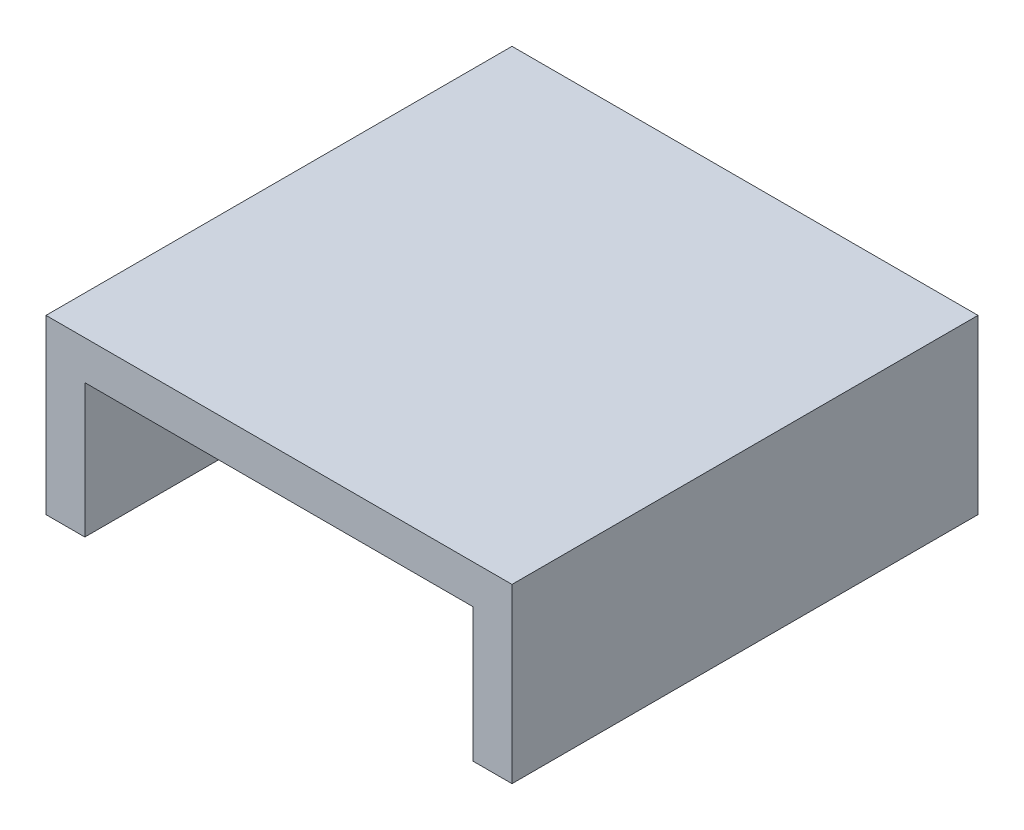
SolidWorks part; units mm, degrees
ref_plane "Front Plane" through (0, 0, 0) normal (0, 0, 1) x (1, 0, 0)
ref_plane "Top Plane" through (0, 0, 0) normal (0, 1, 0) x (1, 0, 0)
ref_plane "Right Plane" through (0, 0, 0) normal (1, 0, 0) x (0, 0, -1)
sketch "Sketch2" plane through (0, 0, 0) normal (0, 0, 1) x (1, 0, 0)
  line L0 (27, 0) -> (-27, 0)
  line L1 (-27, 0) -> (-27, -20)
  line L2 (-27, -20) -> (-22.5, -20)
  line L3 (-22.5, 0) -> (-22.5, -4.5) construction
  line L4 (-22.5, -20) -> (-22.5, -4.5)
  line L5 (27, 0) -> (27, -20)
  line L6 (27, -4.5) -> (22.5, -4.5) construction
  line L7 (-22.5, -4.5) -> (22.5, -4.5)
  line L8 (22.5, -4.5) -> (22.5, -20)
  line L9 (22.5, -20) -> (27, -20)
  point P4 (0, 0)
extrude "Boss-Extrude1" add sketch "Sketch2" along normal blind 54
